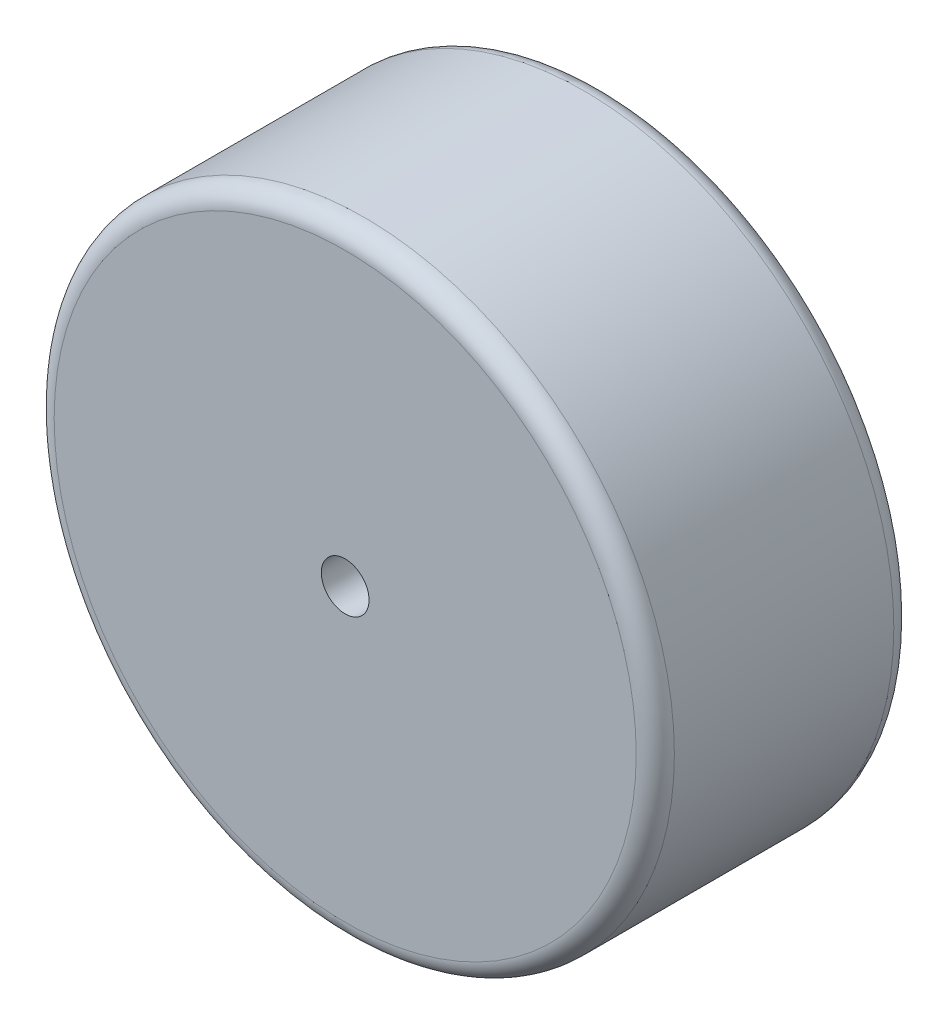
SolidWorks part; units mm, degrees
material "Rubber"
ref_plane "Front Plane" through (0, 0, 0) normal (0, 0, 1) x (1, 0, 0)
ref_plane "Top Plane" through (0, 0, 0) normal (0, 1, 0) x (1, 0, 0)
ref_plane "Right Plane" through (0, 0, 0) normal (1, 0, 0) x (0, 0, -1)
sketch "Sketch1" plane through (0, 0, 0) normal (0, 0, 1) x (1, 0, 0)
  circle A0 centre (0, 0) radius 32.5
  dimension "D1" = 65
extrude "Boss-Extrude1" add sketch "Sketch1" along normal mid plane 27
fillet "Fillet1" radius 2 2 edges at (32.5, 0, 13.5) (32.5, 0, -13.5)
sketch "Sketch2" plane through (0, 0, 13.5) normal (0, 0, 1) x (1, 0, 0)
  circle A0 centre (0, 0) radius 2.5
  dimension "D1" = 5
extrude "Cut-Extrude1" cut sketch "Sketch2" against normal through all
